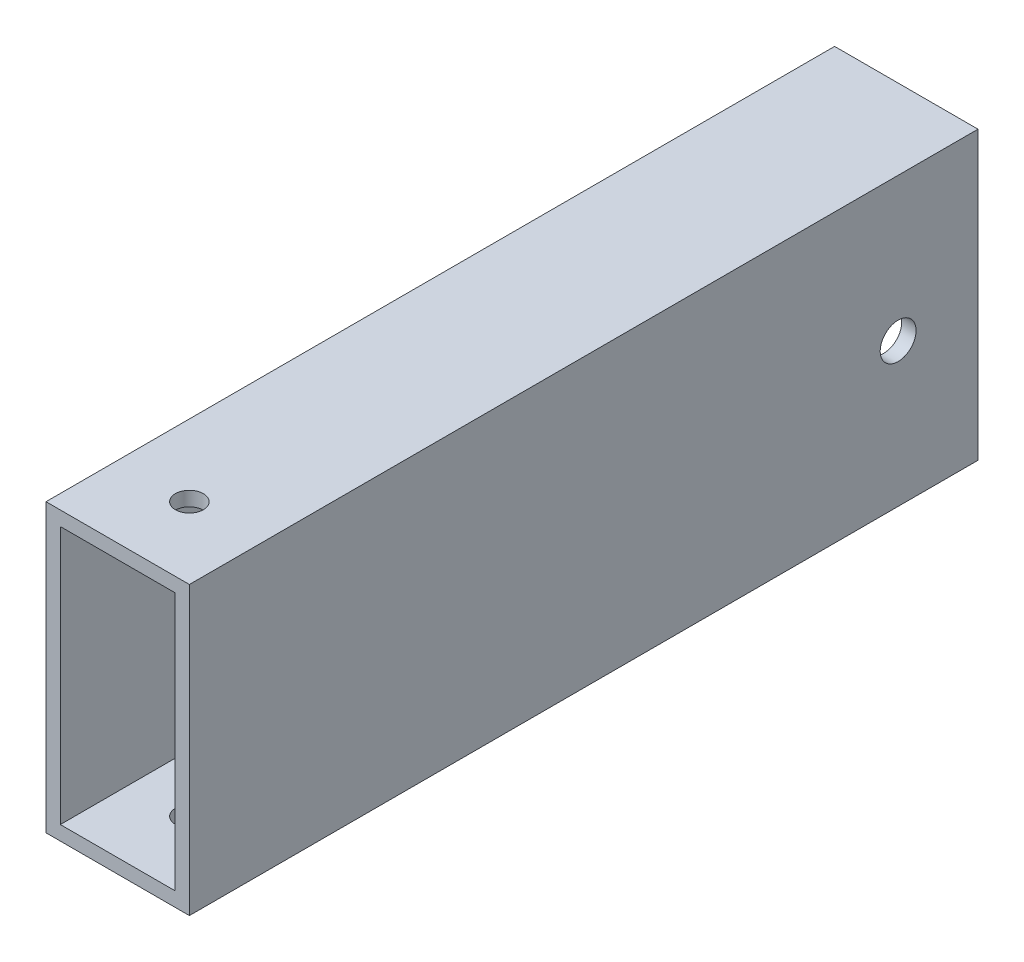
SolidWorks part; units mm, degrees
ref_plane "Front Plane" through (0, 0, 0) normal (0, 0, 1) x (1, 0, 0)
ref_plane "Top Plane" through (0, 0, 0) normal (0, 1, 0) x (1, 0, 0)
ref_plane "Right Plane" through (0, 0, 0) normal (1, 0, 0) x (0, 0, -1)
sketch "Sketch1" plane through (0, 0, 0) normal (0, 0, 1) x (1, 0, 0)
  line L1 (-12.7, -25.4) -> (12.7, -25.4)
  line L2 (-12.7, -25.4) -> (-12.7, 25.4)
  line L3 (-12.7, 25.4) -> (12.7, 25.4)
  line L4 (12.7, -25.4) -> (12.7, 25.4)
  line L5 (-12.7, -25.4) -> (12.7, 25.4) construction
  line L6 (-12.7, 25.4) -> (12.7, -25.4) construction
  point P0 (0, 0)
  dimension "D1" = 25.4
  dimension "D2" = 50.8
extrude "Extrude-Thin1" add sketch "Sketch1" along normal mid plane 139.7 thin thin type one direction reverse wall 2.54
sketch "Sketch2" plane through (12.7, 0, 0) normal (1, 0, 0) x (0, 0, -1)
  line L0 (-69.85, -25.4) -> (-69.85, 25.4) construction
  circle A0 centre (55.7022, 0) radius 3.175
  dimension "D2" = 6.35
  dimension "D1" = 125.5522
extrude "Cut-Extrude1" cut sketch "Sketch2" against normal through all
sketch "Sketch4" plane through (0, 25.4, 0) normal (0, 1, 0) x (1, 0, 0)
  circle A0 centre (0, -57.15) radius 2.4765
extrude "Cut-Extrude3" cut sketch "Sketch4" against normal through all
